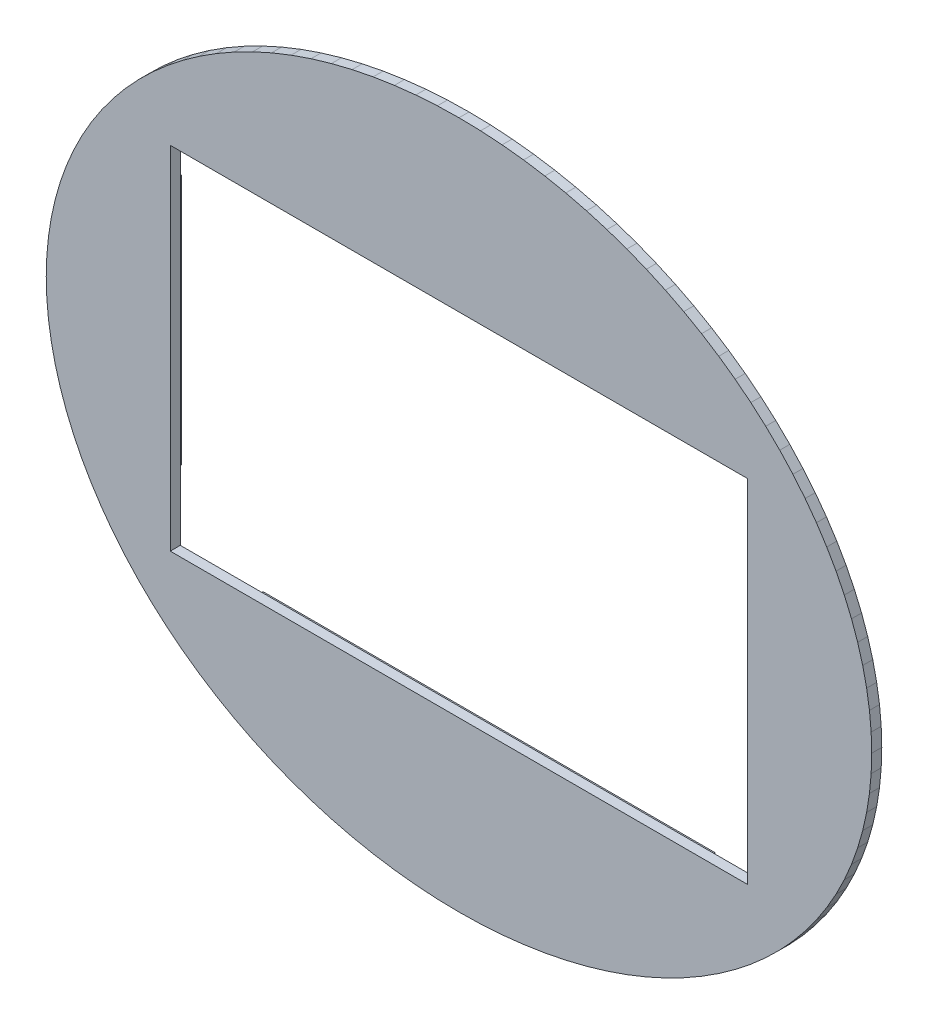
SolidWorks part; units mm, degrees
ref_plane "Front Plane" through (0, 0, 0) normal (0, 0, 1) x (1, 0, 0)
ref_plane "Top Plane" through (0, 0, 0) normal (0, 1, 0) x (1, 0, 0)
ref_plane "Right Plane" through (0, 0, 0) normal (1, 0, 0) x (0, 0, -1)
ref_plane "Plane1" through (0, 0, 66500) normal (0, 0, -1) x (-1, 0, 0)
sketch "Sketch1" plane through (0, 0, 66500) normal (0, 0, -1) x (-1, 0, 0)
  line L0 (41099.9985, 59322.7005) -> (37318.0008, 61033.9012)
  line L1 (37318.0008, 61033.9012) -> (33433.7997, 62577.8999)
  line L2 (33433.7997, 62577.8999) -> (29457.7999, 63950.2983)
  line L3 (29457.7999, 63950.2983) -> (25401.1993, 65147.3999)
  line L4 (25401.1993, 65147.3999) -> (21274.9004, 66165.9012)
  line L5 (21274.9004, 66165.9012) -> (17090.2996, 67003.0975)
  line L6 (17090.2996, 67003.0975) -> (12858.9001, 67656.601)
  line L7 (12858.9001, 67656.601) -> (8592.2403, 68124.7025)
  line L8 (8592.2403, 68124.7025) -> (4302.0201, 68406.0974)
  line L9 (4302.0201, 68406.0974) -> (0, 68500)
  line L10 (0, 68500) -> (-4302.0201, 68406.0974)
  line L11 (-4302.0201, 68406.0974) -> (-8592.2403, 68124.7025)
  line L12 (-8592.2403, 68124.7025) -> (-12858.9001, 67656.601)
  line L13 (-12858.9001, 67656.601) -> (-17090.2996, 67003.0975)
  line L14 (-17090.2996, 67003.0975) -> (-21274.9004, 66165.9012)
  line L15 (-21274.9004, 66165.9012) -> (-25401.1993, 65147.3999)
  line L16 (-25401.1993, 65147.3999) -> (-29457.7999, 63950.2983)
  line L17 (-29457.7999, 63950.2983) -> (-33433.7997, 62577.8999)
  line L18 (-33433.7997, 62577.8999) -> (-37318.0008, 61033.9012)
  line L19 (-37318.0008, 61033.9012) -> (-41099.9985, 59322.7005)
  line L20 (-41099.9985, 59322.7005) -> (-44769.2986, 57448.8983)
  line L21 (-44769.2986, 57448.8983) -> (-48315.8989, 55417.7017)
  line L22 (-48315.8989, 55417.7017) -> (-51730.0987, 53234.5009)
  line L23 (-51730.0987, 53234.5009) -> (-55002.4986, 50905.3993)
  line L24 (-55002.4986, 50905.3993) -> (-58124.1989, 48436.7981)
  line L25 (-58124.1989, 48436.7981) -> (-61086.4983, 45835.3996)
  line L26 (-61086.4983, 45835.3996) -> (-63881.4011, 43108.3984)
  line L27 (-63881.4011, 43108.3984) -> (-66501.1978, 40263.3018)
  line L28 (-66501.1978, 40263.3018) -> (-68938.6978, 37307.8003)
  line L29 (-68938.6978, 37307.8003) -> (-71187.3016, 34250)
  line L30 (-71187.3016, 34250) -> (-73240.6998, 31098.3009)
  line L31 (-73240.6998, 31098.3009) -> (-75093.399, 27861.4998)
  line L32 (-75093.399, 27861.4998) -> (-76740.303, 24548.2006)
  line L33 (-76740.303, 24548.2006) -> (-78176.8036, 21167.6998)
  line L34 (-78176.8036, 21167.6998) -> (-79399.1013, 17729.0993)
  line L35 (-79399.1013, 17729.0993) -> (-80403.7018, 14241.9996)
  line L36 (-80403.7018, 14241.9996) -> (-81188.0035, 10715.8003)
  line L37 (-81188.0035, 10715.8003) -> (-81749.7025, 7160.2001)
  line L38 (-81749.7025, 7160.2001) -> (-82087.3032, 3585.0101)
  line L39 (-82087.3032, 3585.0101) -> (-82199.9969, 0)
  line L40 (-82199.9969, 0) -> (-82087.3032, -3585.0101)
  line L41 (-82087.3032, -3585.0101) -> (-81749.7025, -7160.2001)
  line L42 (-81749.7025, -7160.2001) -> (-81188.0035, -10715.8003)
  line L43 (-81188.0035, -10715.8003) -> (-80403.7018, -14241.9996)
  line L44 (-80403.7018, -14241.9996) -> (-79399.1013, -17729.0993)
  line L45 (-79399.1013, -17729.0993) -> (-78176.8036, -21167.6998)
  line L46 (-78176.8036, -21167.6998) -> (-76740.303, -24548.2006)
  line L47 (-76740.303, -24548.2006) -> (-75093.399, -27861.4998)
  line L48 (-75093.399, -27861.4998) -> (-73240.6998, -31098.3009)
  line L49 (-73240.6998, -31098.3009) -> (-71187.3016, -34250)
  line L50 (-71187.3016, -34250) -> (-68938.6978, -37307.8003)
  line L51 (-68938.6978, -37307.8003) -> (-66501.1978, -40263.3018)
  line L52 (-66501.1978, -40263.3018) -> (-63881.4011, -43108.3984)
  line L53 (-63881.4011, -43108.3984) -> (-61086.4983, -45835.3996)
  line L54 (-61086.4983, -45835.3996) -> (-58124.1989, -48436.7981)
  line L55 (-58124.1989, -48436.7981) -> (-55002.4986, -50905.3993)
  line L56 (-55002.4986, -50905.3993) -> (-51730.0987, -53234.5009)
  line L57 (-51730.0987, -53234.5009) -> (-48315.8989, -55417.7017)
  line L58 (-48315.8989, -55417.7017) -> (-44769.2986, -57448.8983)
  line L59 (-44769.2986, -57448.8983) -> (-41099.9985, -59322.7005)
  line L60 (-41099.9985, -59322.7005) -> (-37318.0008, -61033.9012)
  line L61 (-37318.0008, -61033.9012) -> (-33433.7997, -62577.8999)
  line L62 (-33433.7997, -62577.8999) -> (-29457.7999, -63950.2983)
  line L63 (-29457.7999, -63950.2983) -> (-25401.1993, -65147.3999)
  line L64 (-25401.1993, -65147.3999) -> (-21274.9004, -66165.9012)
  line L65 (-21274.9004, -66165.9012) -> (-17090.2996, -67003.0975)
  line L66 (-17090.2996, -67003.0975) -> (-12858.9001, -67656.601)
  line L67 (-12858.9001, -67656.601) -> (-8592.2403, -68124.7025)
  line L68 (-8592.2403, -68124.7025) -> (-4302.0201, -68406.0974)
  line L69 (-4302.0201, -68406.0974) -> (0, -68500)
  line L70 (0, -68500) -> (4302.0201, -68406.0974)
  line L71 (4302.0201, -68406.0974) -> (8592.2403, -68124.7025)
  line L72 (8592.2403, -68124.7025) -> (12858.9001, -67656.601)
  line L73 (12858.9001, -67656.601) -> (17090.2996, -67003.0975)
  line L74 (17090.2996, -67003.0975) -> (21274.9004, -66165.9012)
  line L75 (21274.9004, -66165.9012) -> (25401.1993, -65147.3999)
  line L76 (25401.1993, -65147.3999) -> (29457.7999, -63950.2983)
  line L77 (29457.7999, -63950.2983) -> (33433.7997, -62577.8999)
  line L78 (33433.7997, -62577.8999) -> (37318.0008, -61033.9012)
  line L79 (37318.0008, -61033.9012) -> (41099.9985, -59322.7005)
  line L80 (41099.9985, -59322.7005) -> (44769.2986, -57448.8983)
  line L81 (44769.2986, -57448.8983) -> (48315.8989, -55417.7017)
  line L82 (48315.8989, -55417.7017) -> (51730.0987, -53234.5009)
  line L83 (51730.0987, -53234.5009) -> (55002.4986, -50905.3993)
  line L84 (55002.4986, -50905.3993) -> (58124.1989, -48436.7981)
  line L85 (58124.1989, -48436.7981) -> (61086.4983, -45835.3996)
  line L86 (61086.4983, -45835.3996) -> (63881.4011, -43108.3984)
  line L87 (63881.4011, -43108.3984) -> (66501.1978, -40263.3018)
  line L88 (66501.1978, -40263.3018) -> (68938.6978, -37307.8003)
  line L89 (68938.6978, -37307.8003) -> (71187.3016, -34250)
  line L90 (71187.3016, -34250) -> (73240.6998, -31098.3009)
  line L91 (73240.6998, -31098.3009) -> (75093.399, -27861.4998)
  line L92 (75093.399, -27861.4998) -> (76740.303, -24548.2006)
  line L93 (76740.303, -24548.2006) -> (78176.8036, -21167.6998)
  line L94 (78176.8036, -21167.6998) -> (79399.1013, -17729.0993)
  line L95 (79399.1013, -17729.0993) -> (80403.7018, -14241.9996)
  line L96 (80403.7018, -14241.9996) -> (81188.0035, -10715.8003)
  line L97 (81188.0035, -10715.8003) -> (81749.7025, -7160.2001)
  line L98 (81749.7025, -7160.2001) -> (82087.3032, -3585.0101)
  line L99 (82087.3032, -3585.0101) -> (82199.9969, 0)
  line L100 (82199.9969, 0) -> (82087.3032, 3585.0101)
  line L101 (82087.3032, 3585.0101) -> (81749.7025, 7160.2001)
  line L102 (81749.7025, 7160.2001) -> (81188.0035, 10715.8003)
  line L103 (81188.0035, 10715.8003) -> (80403.7018, 14241.9996)
  line L104 (80403.7018, 14241.9996) -> (79399.1013, 17729.0993)
  line L105 (79399.1013, 17729.0993) -> (78176.8036, 21167.6998)
  line L106 (78176.8036, 21167.6998) -> (76740.303, 24548.2006)
  line L107 (76740.303, 24548.2006) -> (75093.399, 27861.4998)
  line L108 (75093.399, 27861.4998) -> (73240.6998, 31098.3009)
  line L109 (73240.6998, 31098.3009) -> (71187.3016, 34250)
  line L110 (71187.3016, 34250) -> (68938.6978, 37307.8003)
  line L111 (68938.6978, 37307.8003) -> (66501.1978, 40263.3018)
  line L112 (66501.1978, 40263.3018) -> (63881.4011, 43108.3984)
  line L113 (63881.4011, 43108.3984) -> (61086.4983, 45835.3996)
  line L114 (61086.4983, 45835.3996) -> (58124.1989, 48436.7981)
  line L115 (58124.1989, 48436.7981) -> (55002.4986, 50905.3993)
  line L116 (55002.4986, 50905.3993) -> (51730.0987, 53234.5009)
  line L117 (51730.0987, 53234.5009) -> (48315.8989, 55417.7017)
  line L118 (48315.8989, 55417.7017) -> (44769.2986, 57448.8983)
  line L119 (44769.2986, 57448.8983) -> (41099.9985, 59322.7005)
extrude "Boss-Extrude1" add sketch "Sketch1" against normal blind 2000
sketch "Sketch2" plane through (0, 0, 68500) normal (0, 0, 1) x (1, 0, 0)
  line L0 (-57500, -35000) -> (57500, -35000)
  line L1 (57500, -35000) -> (57500, 35000)
  line L2 (57500, 35000) -> (-57500, 35000)
  line L3 (-57500, 35000) -> (-57500, -35000)
extrude "Cut-Extrude1" cut sketch "Sketch2" against normal through all
sketch "Sketch3" plane through (0, 0, 66500) normal (0, 0, -1) x (-1, 0, 0)
  line L0 (61250, -25000) -> (61250, 25000)
  line L1 (61250, 25000) -> (63500, 25000)
  line L2 (63500, 25000) -> (63500, -25000)
  line L3 (63500, -25000) -> (61250, -25000)
extrude "Boss-Extrude2" add sketch "Sketch3" along normal blind 4000
sketch "Sketch4" plane through (0, 0, 66500) normal (0, 0, -1) x (-1, 0, 0)
  line L0 (-45000, 38750) -> (-45000, 41000)
  line L1 (-45000, 41000) -> (45000, 41000)
  line L2 (45000, 41000) -> (45000, 38750)
  line L3 (45000, 38750) -> (-45000, 38750)
extrude "Boss-Extrude3" add sketch "Sketch4" along normal blind 4000
sketch "Sketch5" plane through (0, 0, 66500) normal (0, 0, -1) x (-1, 0, 0)
  line L0 (-45000, -41000) -> (-45000, -38750)
  line L1 (-45000, -38750) -> (45000, -38750)
  line L2 (45000, -38750) -> (45000, -41000)
  line L3 (45000, -41000) -> (-45000, -41000)
extrude "Boss-Extrude4" add sketch "Sketch5" along normal blind 4000
sketch "Sketch6" plane through (0, 0, 66500) normal (0, 0, -1) x (-1, 0, 0)
  line L0 (-63500, -25000) -> (-63500, 25000)
  line L1 (-63500, 25000) -> (-61250, 25000)
  line L2 (-61250, 25000) -> (-61250, -25000)
  line L3 (-61250, -25000) -> (-63500, -25000)
extrude "Boss-Extrude5" add sketch "Sketch6" along normal blind 4000
scale "Scale4" scale about centroid uniform scaling yes scale factor 0.001
sketch "Sketch17" plane through (0, 0, 67152.2803) normal (0, 0, -1) x (-1, 0, 0)
  line L1 (-61.25, -25) -> (-65.25, -25)
  line L2 (-61.25, -25) -> (-61.25, 25)
  line L3 (-61.25, 25) -> (-65.25, 25)
  line L4 (-65.25, -25) -> (-65.25, 25)
  dimension "D1" = 50
  dimension "D2" = 4
extrude "Boss-Extrude7" add sketch "Sketch17" along normal blind 4 contours L2 L1 L4 L3
sketch "Sketch18" plane through (0, 0, 67148.2803) normal (0, 0, -1) x (-1, 0, 0)
  line L0 (-61.25, -25) -> (-61.25, 25) construction
  line L1 (-61.25, 25) -> (-65.25, 25) construction
  circle A0 centre (-63.25, 0) radius 1.25
  dimension "D1" = 2.5
  dimension "D2" = 2
  dimension "D3" = 25
hole_wizard "#40 (0.098) Diameter Hole1" positions "Sketch19" profile "Sketch20" hole size "#40" standard "ANSI Inch"
sketch "Sketch19" plane through (0, 0, 67148.2803) normal (0, 0, -1) x (-1, 0, 0)
  point P0 (-63.25, 0)
sketch "Sketch20" plane through (63.25, 0, 67148.2803) normal (1, 0, 0) x (0, 1, 0)
  line L0 (0, 0) -> (0, 3.7511)
  line L1 (0, 3.7511) -> (1.25, 3)
  line L2 (1.25, 3) -> (1.25, 0)
  line L5 (1.25, 0) -> (0, 0)
  line L10 (0, 3.7511) -> (-1.25, 3) construction
  line L11 (0, -6.35) -> (0, 107.95) construction
  dimension "Hole Dia." = 2.5
  dimension "Hole Depth" = 3
  dimension "Drill Angle" = 118
sketch "Sketch21" plane through (0, 0, 67152.2803) normal (0, 0, -1) x (-1, 0, 0)
  line L1 (-45, 38.75) -> (45, 38.75)
  line L2 (-45, 38.75) -> (-45, 42.75)
  line L3 (-45, 42.75) -> (45, 42.75)
  line L4 (45, 38.75) -> (45, 42.75)
  dimension "D1" = 90
  dimension "D2" = 4
extrude "Boss-Extrude8" add sketch "Sketch21" along normal blind 4
sketch "Sketch22" plane through (0, 0, 67152.2803) normal (0, 0, -1) x (-1, 0, 0)
  line L1 (61.25, -25) -> (65.25, -25)
  line L2 (61.25, -25) -> (61.25, 25)
  line L3 (61.25, 25) -> (65.25, 25)
  line L4 (65.25, -25) -> (65.25, 25)
  dimension "D1" = 50
  dimension "D2" = 4
extrude "Boss-Extrude9" add sketch "Sketch22" along normal blind 4
sketch "Sketch23" plane through (0, 0, 67152.2803) normal (0, 0, -1) x (-1, 0, 0)
  line L1 (-45, -38.75) -> (45, -38.75)
  line L2 (-45, -38.75) -> (-45, -42.75)
  line L3 (-45, -42.75) -> (45, -42.75)
  line L4 (45, -38.75) -> (45, -42.75)
  dimension "D1" = 90
  dimension "D2" = 4
extrude "Boss-Extrude10" add sketch "Sketch23" along normal blind 4
sketch "Sketch45" plane through (0, 0, 67148.2803) normal (0, 0, -1) x (-1, 0, 0)
  line L0 (-45, -42.75) -> (45, -42.75) construction
  line L1 (45, -42.75) -> (45, -38.75) construction
  circle A0 centre (0, -40.75) radius 1.25
  dimension "D1" = 2
  dimension "D2" = 45
hole_wizard "M2.5 Clearance Hole3" positions "Sketch48" profile "Sketch47" hole size "M2.5" standard "ANSI Metric"
sketch "Sketch48" plane through (0, 0, 67148.2803) normal (0, 0, -1) x (-1, 0, 0)
  point P0 (0, -40.75)
sketch "Sketch47" plane through (0, -40.75, 67148.2803) normal (1, 0, 0) x (0, 1, 0)
  line L0 (0, 0) -> (0, 3.8712)
  line L1 (0, 3.8712) -> (1.45, 3)
  line L2 (1.45, 3) -> (1.45, 0)
  line L5 (1.45, 0) -> (0, 0)
  line L10 (0, 3.8712) -> (-1.45, 3) construction
  line L11 (0, -6.35) -> (0, 107.95) construction
  dimension "Hole Dia." = 2.9
  dimension "Hole Depth" = 3
  dimension "Drill Angle" = 118
sketch "Sketch51" plane through (0, 0, 67148.2803) normal (0, 0, -1) x (-1, 0, 0)
  line L1 (-45, 38.75) -> (45, 38.75) construction
  line L2 (45, 38.75) -> (45, 42.75) construction
  circle A0 centre (0, 40.75) radius 1.25
  dimension "D1" = 2.5
  dimension "D2" = 2
  dimension "D3" = 45
hole_wizard "M2.5 Clearance Hole4" positions "Sketch52" profile "Sketch53" hole size "M2.5" standard "ANSI Metric"
sketch "Sketch52" plane through (0, 0, 67148.2803) normal (0, 0, -1) x (-1, 0, 0)
  point P0 (0, 40.75)
sketch "Sketch53" plane through (0, 40.75, 67148.2803) normal (1, 0, 0) x (0, 1, 0)
  line L0 (0, 0) -> (0, 3.8712)
  line L1 (0, 3.8712) -> (1.45, 3)
  line L2 (1.45, 3) -> (1.45, 0)
  line L5 (1.45, 0) -> (0, 0)
  line L10 (0, 3.8712) -> (-1.45, 3) construction
  line L11 (0, -6.35) -> (0, 107.95) construction
  dimension "Hole Dia." = 2.9
  dimension "Hole Depth" = 3
  dimension "Drill Angle" = 118
sketch "Sketch59" plane through (0, 0, 67148.2803) normal (0, 0, -1) x (-1, 0, 0)
  line L0 (65.25, -25) -> (65.25, 25) construction
  line L3 (61.25, -25) -> (65.25, -25) construction
  circle A0 centre (63.25, 0) radius 1.25
  dimension "D1" = 2.5
  dimension "D2" = 2
  dimension "D3" = 25
hole_wizard "M2.5 Clearance Hole5" positions "Sketch60" profile "Sketch61" hole size "M2.5" standard "ANSI Metric"
sketch "Sketch60" plane through (0, 0, 67148.2803) normal (0, 0, -1) x (-1, 0, 0)
  point P0 (63.25, 0)
sketch "Sketch61" plane through (-63.25, 0, 67148.2803) normal (1, 0, 0) x (0, 1, 0)
  line L0 (0, 0) -> (0, 3.8712)
  line L1 (0, 3.8712) -> (1.45, 3)
  line L2 (1.45, 3) -> (1.45, 0)
  line L5 (1.45, 0) -> (0, 0)
  line L10 (0, 3.8712) -> (-1.45, 3) construction
  line L11 (0, -6.35) -> (0, 107.95) construction
  dimension "Hole Dia." = 2.9
  dimension "Hole Depth" = 3
  dimension "Drill Angle" = 118
